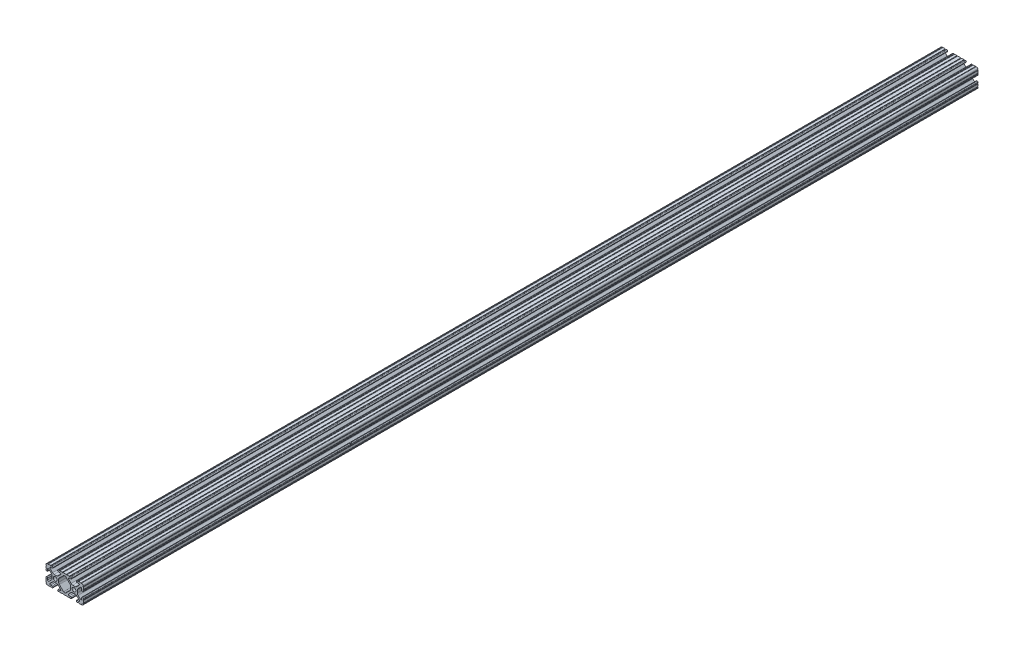
SolidWorks part; units mm, degrees
ref_plane "Front Plane" through (0, 0, 0) normal (0, 0, 1) x (1, 0, 0)
ref_plane "Top Plane" through (0, 0, 0) normal (0, 1, 0) x (1, 0, 0)
ref_plane "Right Plane" through (0, 0, 0) normal (1, 0, 0) x (0, 0, -1)
sketch "Sketch1" plane through (0, 0, 0) normal (0, 0, 1) x (1, 0, 0)
  line L0 (-7.2595, -3.8694) -> (-1.5457, -9.5728)
  line L1 (-8.1915, 1.6223) -> (-8.1915, -1.6223)
  line L2 (-1.504, 9.5765) -> (-7.252, 3.8768)
  line L3 (0.5515, 10.033) -> (-0.3952, 10.033)
  line L4 (7.2829, 3.8459) -> (1.6756, 9.5611)
  line L5 (8.1915, -1.6223) -> (8.1915, 1.6223)
  line L6 (1.5457, -9.5728) -> (7.2595, -3.8694)
  line L7 (-0.4332, -10.033) -> (0.4332, -10.033)
  line L8 (18.0171, 12.7) -> (16.9875, 12.7)
  line L9 (15.9385, 11.651) -> (15.9385, 11.5392)
  line L10 (16.9875, 10.4902) -> (19.1164, 10.4902)
  line L11 (19.8441, 8.7652) -> (16.619, 5.4551)
  line L12 (14.3449, 4.4958) -> (11.0833, 4.4958)
  line L13 (8.817, 5.4472) -> (5.5642, 8.7627)
  line L14 (6.2894, 10.4902) -> (8.4125, 10.4902)
  line L15 (9.4615, 11.5392) -> (9.4615, 11.651)
  line L16 (8.4125, 12.7) -> (7.3829, 12.7)
  line L17 (6.3669, 12.7) -> (3.1496, 12.7)
  line L18 (2.1336, 12.7) -> (-2.1336, 12.7)
  line L19 (-3.1496, 12.7) -> (-6.3669, 12.7)
  line L20 (-7.3829, 12.7) -> (-8.4125, 12.7)
  line L21 (-9.4615, 11.651) -> (-9.4615, 11.5392)
  line L22 (-8.4125, 10.4902) -> (-6.2836, 10.4902)
  line L23 (-5.5326, 8.6661) -> (-8.81, 5.4163)
  line L24 (-11.0455, 4.4958) -> (-14.3545, 4.4958)
  line L25 (-16.59, 5.4163) -> (-19.8674, 8.6661)
  line L26 (-19.1164, 10.4902) -> (-16.9875, 10.4902)
  line L27 (-15.9385, 11.5392) -> (-15.9385, 11.651)
  line L28 (-16.9875, 12.7) -> (-18.0171, 12.7)
  line L29 (-19.0331, 12.7) -> (-22.2504, 12.7)
  line L30 (-25.4, 9.5504) -> (-25.4, 6.3331)
  line L31 (-25.4, 5.3171) -> (-25.4, 4.2375)
  line L32 (-24.401, 3.2385) -> (-24.2392, 3.2385)
  line L33 (-23.1902, 4.2875) -> (-23.1902, 6.3347)
  line L34 (-21.434, 7.0665) -> (-18.148, 3.8082)
  line L35 (-17.2085, 1.5536) -> (-17.2085, -1.6952)
  line L36 (-18.1405, -3.9423) -> (-21.4316, -7.2274)
  line L37 (-23.1902, -6.498) -> (-23.1902, -4.2875)
  line L38 (-24.2392, -3.2385) -> (-24.351, -3.2385)
  line L39 (-25.4, -4.2875) -> (-25.4, -5.3171)
  line L40 (-25.4, -6.3331) -> (-25.4, -9.5504)
  line L41 (-22.2504, -12.7) -> (-19.0331, -12.7)
  line L42 (-18.0171, -12.7) -> (-16.9875, -12.7)
  line L43 (-15.9384, -11.651) -> (-15.9384, -11.5392)
  line L44 (-16.9875, -10.4902) -> (-19.1164, -10.4902)
  line L45 (-19.8341, -8.7551) -> (-16.4966, -5.4237)
  line L46 (-14.2536, -4.4958) -> (-11.1464, -4.4958)
  line L47 (-8.9034, -5.4237) -> (-5.5659, -8.7551)
  line L48 (-6.2836, -10.4902) -> (-8.4125, -10.4902)
  line L49 (-9.4616, -11.5392) -> (-9.4616, -11.651)
  line L50 (-8.4125, -12.7) -> (-7.3829, -12.7)
  line L51 (-6.3669, -12.7) -> (-3.1496, -12.7)
  line L52 (-2.1336, -12.7) -> (2.1336, -12.7)
  line L53 (3.1496, -12.7) -> (6.3669, -12.7)
  line L54 (7.3829, -12.7) -> (8.4125, -12.7)
  line L55 (9.4616, -11.651) -> (9.4616, -11.5392)
  line L56 (8.4125, -10.4902) -> (6.2894, -10.4902)
  line L57 (5.4807, -8.5353) -> (8.5979, -5.4237)
  line L58 (10.8409, -4.4958) -> (14.1026, -4.4958)
  line L59 (16.1879, -5.2766) -> (19.8682, -8.4822)
  line L60 (19.1164, -10.4902) -> (16.9875, -10.4902)
  line L61 (15.9384, -11.5392) -> (15.9384, -11.651)
  line L62 (16.9875, -12.7) -> (18.0171, -12.7)
  line L63 (19.0331, -12.7) -> (22.2504, -12.7)
  line L64 (25.4, -9.5504) -> (25.4, -6.3331)
  line L65 (25.4, -5.3171) -> (25.4, -4.2375)
  line L66 (24.401, -3.2385) -> (24.1892, -3.2385)
  line L67 (23.1902, -4.2375) -> (23.1902, -6.1559)
  line L68 (21.584, -6.8869) -> (18.2982, -4.025)
  line L69 (17.2085, -1.6308) -> (17.2085, 1.6308)
  line L70 (18.1094, 3.8465) -> (21.5263, 7.3534)
  line L71 (23.1902, 6.6769) -> (23.1902, 4.2375)
  line L72 (24.1892, 3.2385) -> (24.401, 3.2385)
  line L73 (25.4, 4.2375) -> (25.4, 5.3171)
  line L74 (25.4, 6.3332) -> (25.4, 9.5504)
  line L75 (22.2504, 12.7) -> (19.0331, 12.7)
  circle A0 centre (-12.7, 0) radius 2.6035
  circle A1 centre (12.7, 0) radius 2.6035
  arc A2 (-1.5457, -9.5728) -> (-0.4332, -10.033) centre (-0.4332, -8.4582) ccw
  arc A3 (-8.1915, -1.6223) -> (-7.2595, -3.8694) centre (-5.0165, -1.6223) ccw
  arc A4 (-7.252, 3.8768) -> (-8.1915, 1.6223) centre (-5.0165, 1.6223) ccw
  arc A5 (-0.3952, 10.033) -> (-1.504, 9.5765) centre (-0.3952, 8.4582) ccw
  arc A6 (1.6756, 9.5611) -> (0.5515, 10.033) centre (0.5515, 8.4582) ccw
  arc A7 (8.1915, 1.6223) -> (7.2829, 3.8459) centre (5.0165, 1.6223) ccw
  arc A8 (7.2595, -3.8694) -> (8.1915, -1.6223) centre (5.0165, -1.6223) ccw
  arc A9 (0.4332, -10.033) -> (1.5457, -9.5728) centre (0.4332, -8.4582) ccw
  arc A10 (18.0171, 12.7) -> (19.0331, 12.7) centre (18.5251, 12.7) ccw
  arc A11 (16.9875, 12.7) -> (15.9385, 11.651) centre (16.9875, 11.651) ccw
  arc A12 (15.9385, 11.5392) -> (16.9875, 10.4902) centre (16.9875, 11.5392) ccw
  arc A13 (19.8441, 8.7652) -> (19.1164, 10.4902) centre (19.1164, 9.4742) ccw
  arc A14 (14.3449, 4.4958) -> (16.619, 5.4551) centre (14.3449, 7.6708) ccw
  arc A15 (8.817, 5.4472) -> (11.0833, 4.4958) centre (11.0833, 7.6708) ccw
  arc A16 (6.2894, 10.4902) -> (5.5642, 8.7627) centre (6.2894, 9.4742) ccw
  arc A17 (8.4125, 10.4902) -> (9.4615, 11.5392) centre (8.4125, 11.5392) ccw
  arc A18 (9.4615, 11.651) -> (8.4125, 12.7) centre (8.4125, 11.651) ccw
  arc A19 (6.3669, 12.7) -> (7.3829, 12.7) centre (6.8749, 12.7) ccw
  arc A20 (2.1336, 12.7) -> (3.1496, 12.7) centre (2.6416, 12.7) ccw
  arc A21 (-3.1496, 12.7) -> (-2.1336, 12.7) centre (-2.6416, 12.7) ccw
  arc A22 (-7.3829, 12.7) -> (-6.3669, 12.7) centre (-6.8749, 12.7) ccw
  arc A23 (-8.4125, 12.7) -> (-9.4615, 11.651) centre (-8.4125, 11.651) ccw
  arc A24 (-9.4615, 11.5392) -> (-8.4125, 10.4902) centre (-8.4125, 11.5392) ccw
  arc A25 (-5.5326, 8.6661) -> (-6.2836, 10.4902) centre (-6.2836, 9.4235) ccw
  arc A26 (-11.0455, 4.4958) -> (-8.81, 5.4163) centre (-11.0455, 7.6708) ccw
  arc A27 (-16.59, 5.4163) -> (-14.3545, 4.4958) centre (-14.3545, 7.6708) ccw
  arc A28 (-19.1164, 10.4902) -> (-19.8674, 8.6661) centre (-19.1164, 9.4235) ccw
  arc A29 (-16.9875, 10.4902) -> (-15.9385, 11.5392) centre (-16.9875, 11.5392) ccw
  arc A30 (-15.9385, 11.651) -> (-16.9875, 12.7) centre (-16.9875, 11.651) ccw
  arc A31 (-19.0331, 12.7) -> (-18.0171, 12.7) centre (-18.5251, 12.7) ccw
  arc A32 (-23.2664, 12.6998) -> (-22.2504, 12.7) centre (-22.7584, 12.7) ccw
  arc A33 (-23.2664, 12.6998) -> (-25.3998, 10.5664) centre (-23.2918, 10.5918) ccw
  arc A34 (-25.4, 9.5504) -> (-25.3998, 10.5664) centre (-25.4, 10.0584) ccw
  arc A35 (-25.4, 5.3171) -> (-25.4, 6.3331) centre (-25.4, 5.8251) ccw
  arc A36 (-25.4, 4.2375) -> (-24.401, 3.2385) centre (-24.401, 4.2375) ccw
  arc A37 (-24.2392, 3.2385) -> (-23.1902, 4.2875) centre (-24.2392, 4.2875) ccw
  arc A38 (-21.434, 7.0665) -> (-23.1902, 6.3347) centre (-22.1596, 6.3347) ccw
  arc A39 (-17.2085, 1.5536) -> (-18.148, 3.8082) centre (-20.3835, 1.5536) ccw
  arc A40 (-18.1405, -3.9423) -> (-17.2085, -1.6952) centre (-20.3835, -1.6952) ccw
  arc A41 (-23.1902, -6.498) -> (-21.4316, -7.2274) centre (-22.1596, -6.498) ccw
  arc A42 (-23.1902, -4.2875) -> (-24.2392, -3.2385) centre (-24.2392, -4.2875) ccw
  arc A43 (-24.351, -3.2385) -> (-25.4, -4.2875) centre (-24.351, -4.2875) ccw
  arc A44 (-25.4, -6.3331) -> (-25.4, -5.3171) centre (-25.4, -5.8251) ccw
  arc A45 (-25.3998, -10.5664) -> (-25.4, -9.5504) centre (-25.4, -10.0584) ccw
  arc A46 (-25.3998, -10.5664) -> (-23.2664, -12.6998) centre (-23.2918, -10.5918) ccw
  arc A47 (-22.2504, -12.7) -> (-23.2664, -12.6998) centre (-22.7584, -12.7) ccw
  arc A48 (-18.0171, -12.7) -> (-19.0331, -12.7) centre (-18.5251, -12.7) ccw
  arc A49 (-16.9875, -12.7) -> (-15.9384, -11.651) centre (-16.9875, -11.651) ccw
  arc A50 (-15.9384, -11.5392) -> (-16.9875, -10.4902) centre (-16.9875, -11.5392) ccw
  arc A51 (-19.8341, -8.7551) -> (-19.1164, -10.4902) centre (-19.1164, -9.4742) ccw
  arc A52 (-14.2536, -4.4958) -> (-16.4966, -5.4237) centre (-14.2536, -7.6708) ccw
  arc A53 (-8.9034, -5.4237) -> (-11.1464, -4.4958) centre (-11.1464, -7.6708) ccw
  arc A54 (-6.2836, -10.4902) -> (-5.5659, -8.7551) centre (-6.2836, -9.4742) ccw
  arc A55 (-8.4125, -10.4902) -> (-9.4616, -11.5392) centre (-8.4125, -11.5392) ccw
  arc A56 (-9.4616, -11.651) -> (-8.4125, -12.7) centre (-8.4125, -11.651) ccw
  arc A57 (-6.3669, -12.7) -> (-7.3829, -12.7) centre (-6.8749, -12.7) ccw
  arc A58 (-2.1336, -12.7) -> (-3.1496, -12.7) centre (-2.6416, -12.7) ccw
  arc A59 (3.1496, -12.7) -> (2.1336, -12.7) centre (2.6416, -12.7) ccw
  arc A60 (7.3829, -12.7) -> (6.3669, -12.7) centre (6.8749, -12.7) ccw
  arc A61 (8.4125, -12.7) -> (9.4616, -11.651) centre (8.4125, -11.651) ccw
  arc A62 (9.4616, -11.5392) -> (8.4125, -10.4902) centre (8.4125, -11.5392) ccw
  arc A63 (5.4807, -8.5353) -> (6.2894, -10.4902) centre (6.2894, -9.3455) ccw
  arc A64 (10.8409, -4.4958) -> (8.5979, -5.4237) centre (10.8409, -7.6708) ccw
  arc A65 (16.1879, -5.2766) -> (14.1026, -4.4958) centre (14.1026, -7.6708) ccw
  arc A66 (19.1164, -10.4902) -> (19.8682, -8.4822) centre (19.1164, -9.3455) ccw
  arc A67 (16.9875, -10.4902) -> (15.9384, -11.5392) centre (16.9875, -11.5392) ccw
  arc A68 (15.9384, -11.651) -> (16.9875, -12.7) centre (16.9875, -11.651) ccw
  arc A69 (19.0331, -12.7) -> (18.0171, -12.7) centre (18.5251, -12.7) ccw
  arc A70 (23.2664, -12.6998) -> (22.2504, -12.7) centre (22.7584, -12.7) ccw
  arc A71 (23.2664, -12.6998) -> (25.3998, -10.5664) centre (23.2918, -10.5918) ccw
  arc A72 (25.4, -9.5504) -> (25.3998, -10.5664) centre (25.4, -10.0584) ccw
  arc A73 (25.4, -5.3171) -> (25.4, -6.3331) centre (25.4, -5.8251) ccw
  arc A74 (25.4, -4.2375) -> (24.401, -3.2385) centre (24.401, -4.2375) ccw
  arc A75 (24.1892, -3.2385) -> (23.1902, -4.2375) centre (24.1892, -4.2375) ccw
  arc A76 (21.584, -6.8869) -> (23.1902, -6.1559) centre (22.2207, -6.1559) ccw
  arc A77 (17.2085, -1.6308) -> (18.2982, -4.025) centre (20.3835, -1.6308) ccw
  arc A78 (18.1094, 3.8465) -> (17.2085, 1.6308) centre (20.3835, 1.6308) ccw
  arc A79 (23.1902, 6.6769) -> (21.5263, 7.3534) centre (22.2207, 6.6769) ccw
  arc A80 (23.1902, 4.2375) -> (24.1892, 3.2385) centre (24.1892, 4.2375) ccw
  arc A81 (24.401, 3.2385) -> (25.4, 4.2375) centre (24.401, 4.2375) ccw
  arc A82 (25.4, 6.3332) -> (25.4, 5.3171) centre (25.4, 5.8251) ccw
  arc A83 (25.3998, 10.5664) -> (25.4, 9.5504) centre (25.4, 10.0584) ccw
  arc A84 (25.3998, 10.5664) -> (23.2664, 12.6998) centre (23.2918, 10.5918) ccw
  arc A85 (22.2504, 12.7) -> (23.2664, 12.6998) centre (22.7584, 12.7) ccw
  point P248 (0, 10.033)
extrude "Boss-Extrude1" add sketch "Sketch1" along normal mid plane 1219.2
sketch "Sketch2" plane through (17.2085, 0, 0) normal (1, 0, 0) x (0, 0, -1)
  line L1 (609.6, -1.6308) -> (609.6, 1.6308) construction
  line L2 (0, 0) -> (0, 191.3427) construction
  circle A0 centre (244.47, 0) radius 3.5
  circle A1 centre (-244.47, 0) radius 3.5
  circle A2 centre (396.87, 0) radius 3.5
  circle A3 centre (-396.87, 0) radius 3.5
  dimension "D1" = 7
  dimension "D2" = 365.13
  dimension "D3" = 7
  dimension "D4" = 152.4
extrude "Cut-Extrude1" cut sketch "Sketch2" against normal through all both and the other way through all
